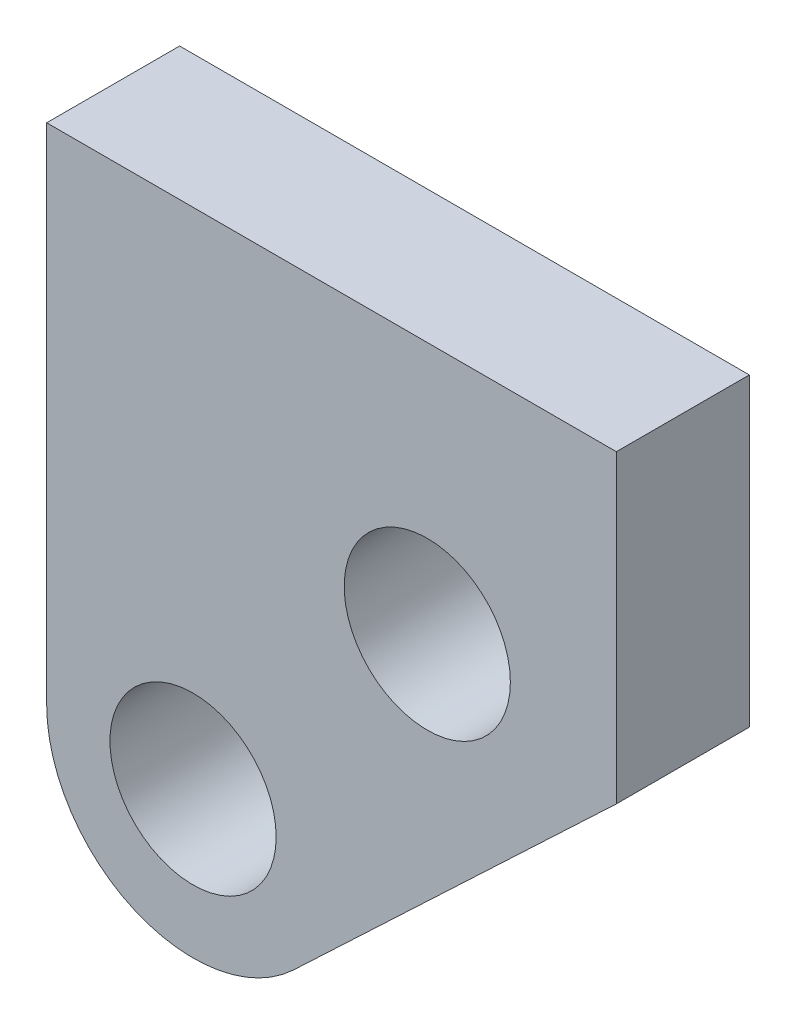
SolidWorks part; units mm, degrees
ref_plane "Plane1" through (0, 0, 0) normal (0, 0, 1) x (1, 0, 0)
ref_plane "Plane2" through (0, 0, 0) normal (0, 1, 0) x (1, 0, 0)
ref_plane "Plane3" through (0, 0, 0) normal (1, 0, 0) x (0, 0, -1)
sketch "Sketch1" plane through (0, 0, 0) normal (0, 0, 1) x (1, 0, 0)
  line L0 (29.7852, -23.1872) -> (54.0595, -0.2389)
  line L1 (54.0595, 22.7057) -> (11.2112, 22.7057)
  line L2 (54.0595, 22.7057) -> (54.0595, -0.2389)
  line L4 (11.2112, 22.7057) -> (11.2112, -15.1864)
  circle A0 centre (22.2214, -15.1864) radius 6.25 construction
  circle A1 centre (39.8373, 3.7044) radius 6.25 construction
  circle A2 centre (22.2214, -15.1864) radius 6.25
  circle A3 centre (39.8373, 3.7044) radius 6.25
  arc A4 (11.2112, -15.1864) -> (29.7852, -23.1872) centre (22.2214, -15.1864) ccw
extrude "Base-Extrude" add sketch "Sketch1" against normal blind 10
